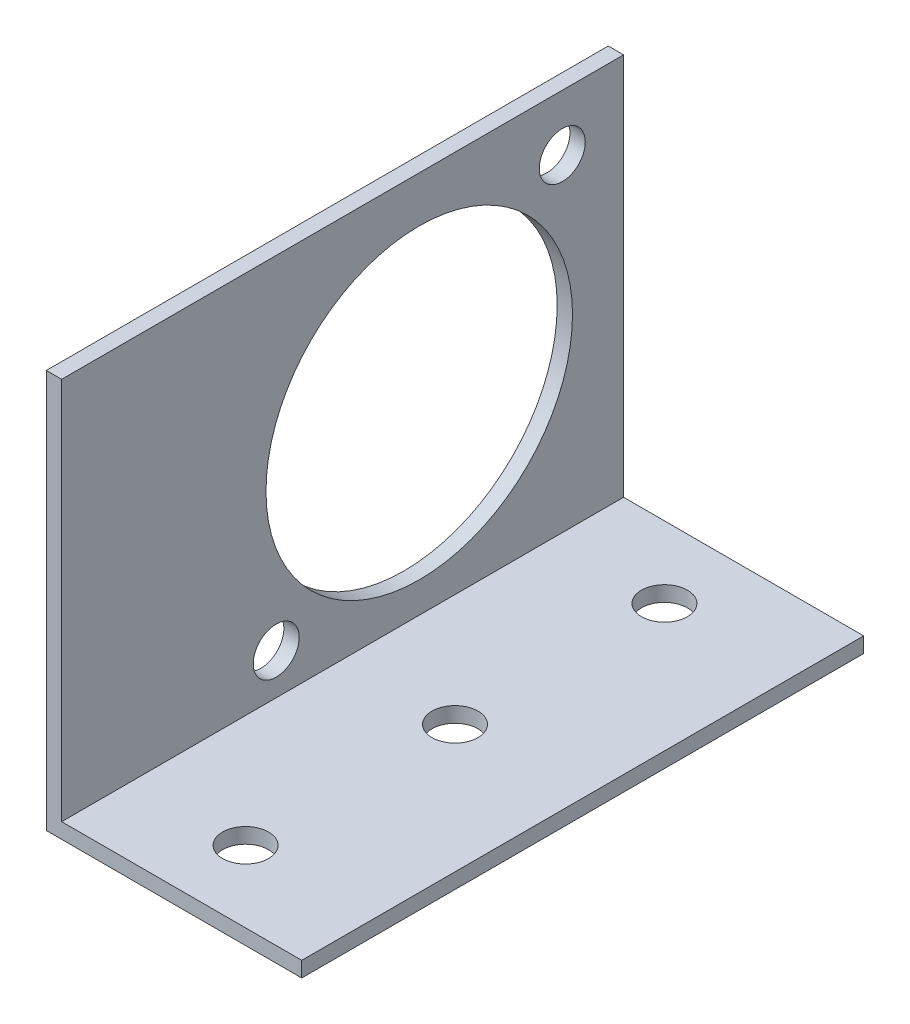
SolidWorks part; units mm, degrees
ref_plane "Plan de face" through (0, 0, 0) normal (0, 0, 1) x (1, 0, 0)
ref_plane "Plan de dessus" through (0, 0, 0) normal (0, 1, 0) x (1, 0, 0)
ref_plane "Plan de droite" through (0, 0, 0) normal (1, 0, 0) x (0, 0, -1)
sketch "Esquisse1" plane through (0, 0, 0) normal (0, 0, 1) x (1, 0, 0)
  line L0 (0, 0) -> (25, 0)
  line L1 (0, 0) -> (0, 39)
  dimension "D1" = 39
  dimension "D2" = 25
extrude "Extru.-Mince1" add sketch "Esquisse1" against normal blind 55 thin thin type one direction wall 1.5
sketch "Esquisse2" plane through (0, 1.5, 0) normal (0, 1, 0) x (-1, 0, 0)
  line L0 (-25, 0) -> (-1.5, 0) construction
  line L1 (-25, -55) -> (-1.5, -55) construction
  line L2 (-25, -55) -> (-25, 0) construction
  point P0 (-12.5, -7)
  point P1 (-12.5, -27.5)
  point P2 (-12.5, -48)
  dimension "D1" = 7
  dimension "D2" = 7
  dimension "D3" = 27.5
  dimension "D4" = 12.5
  dimension "D5" = 12.5
  dimension "D6" = 12.5
hole_wizard "Dégagement M41" positions "Esquisse8" profile "Esquisse9" hole size "M4" standard "ISO" end condition through all
sketch "Esquisse8" plane through (0, 1.5, 0) normal (0, 1, 0) x (-1, 0, 0)
  point P1 (-12.5, -7)
  point P4 (-12.5, -27.5)
  point P7 (-12.5, -48)
sketch "Esquisse9" plane through (12.5, 1.5, -7) normal (1, 0, 0) x (0, 0, 1)
  line L0 (0, 0) -> (0, 1.5)
  line L1 (0, 1.5) -> (2.25, 1.5)
  line L2 (2.25, 1.5) -> (2.25, 0)
  line L5 (2.25, 0) -> (0, 0)
  line L11 (0, -6.35) -> (0, 107.95) construction
  dimension "Diamètre du perçage jusqu'au prochain" = 4.5
  dimension "Profondeur du perçage jusqu'au prochain" = 1.5
sketch "Esquisse10" plane through (1.5, 0, 0) normal (1, 0, 0) x (0, 0, -1)
  line L0 (55, 39) -> (0, 39) construction
  line L1 (0, 1.5) -> (0, 39) construction
  point P0 (35, 19.5)
  point P5 (21, 5.5)
  point P6 (49, 33.5)
  dimension "D1" = 19.5
  dimension "D2" = 35
  dimension "D3" = 49
  dimension "D4" = 5.5
  dimension "D5" = 33.5
  dimension "D6" = 21
hole_wizard "Dégagement M42" positions "Esquisse12" profile "Esquisse11" hole size "M4" standard "ISO" end condition through all
sketch "Esquisse12" plane through (1.5, 0, 0) normal (1, 0, 0) x (0, 0, -1)
  point P1 (49, 33.5)
  point P4 (21, 5.5)
sketch "Esquisse11" plane through (1.5, 33.5, -49) normal (0, 1, 0) x (0, 0, -1)
  line L0 (0, 0) -> (0, 1.5)
  line L1 (0, 1.5) -> (2.25, 1.5)
  line L2 (2.25, 1.5) -> (2.25, 0)
  line L5 (2.25, 0) -> (0, 0)
  line L11 (0, -6.35) -> (0, 107.95) construction
  dimension "Diamètre du perçage jusqu'au prochain" = 4.5
  dimension "Profondeur du perçage jusqu'au prochain" = 1.5
hole_wizard "Dégagement M271" positions "Esquisse14" profile "Esquisse13" hole size "M27" standard "ISO"
sketch "Esquisse14" plane through (1.5, 0, 0) normal (1, 0, 0) x (0, 0, -1)
  point P1 (35, 19.5)
sketch "Esquisse13" plane through (1.5, 19.5, -35) normal (0, 1, 0) x (0, 0, -1)
  line L0 (0, 0) -> (0, 10.5129)
  line L1 (0, 10.5129) -> (15, 1.5)
  line L2 (15, 1.5) -> (15, 0)
  line L5 (15, 0) -> (0, 0)
  line L10 (0, 10.5129) -> (-15, 1.5) construction
  line L11 (0, -6.35) -> (0, 107.95) construction
  dimension "Diamètre du perçage" = 30
  dimension "Profondeur du perçage" = 1.5
  dimension "Angle de pointe" = 118
